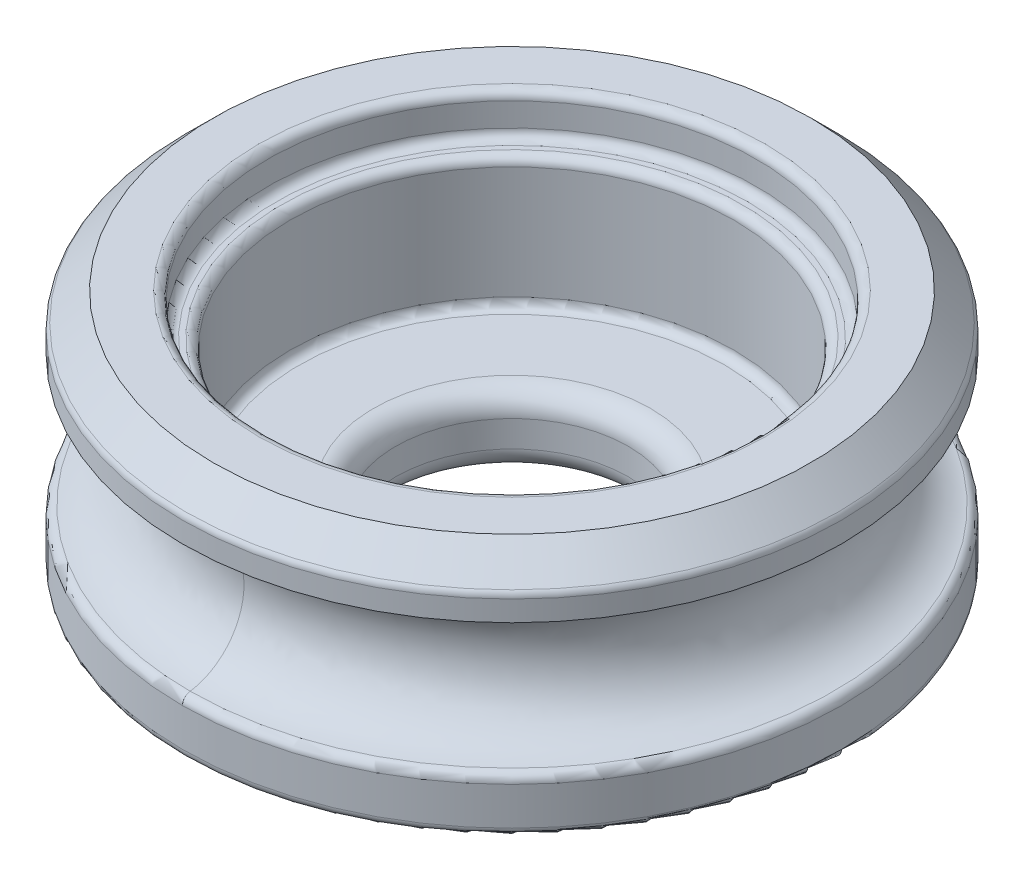
SolidWorks part; units mm, degrees
ref_plane "Front Plane" through (0, 0, 0) normal (0, 0, 1) x (1, 0, 0)
ref_plane "Top Plane" through (0, 0, 0) normal (0, 1, 0) x (1, 0, 0)
ref_plane "Right Plane" through (0, 0, 0) normal (1, 0, 0) x (0, 0, -1)
sketch "Sketch2" plane through (0, 0, 0) normal (0, 1, 0) x (1, 0, 0)
  circle A0 centre (0, 0) radius 6.477 construction
  circle A1 centre (0, 0) radius 9.525
  dimension "D1" = 12.954
  dimension "D2" = 19.05
extrude "Boss-Extrude1" add sketch "Sketch2" along normal blind 6.985
sketch "Sketch3" plane through (0, 6.985, 0) normal (0, 1, 0) x (1, 0, 0)
  circle A0 centre (0, 0) radius 6.4135
  dimension "D1" = 12.827
extrude "Cut-Extrude1" cut sketch "Sketch3" against normal up to surface (6.985 mm away) up to face at (0, 0, 9.525)
sketch "Sketch4" plane through (0, 6.985, 0) normal (0, 1, 0) x (1, 0, 0)
  circle A0 centre (0, 0) radius 7.0723
  dimension "D1" = 14.1446
extrude "Cut-Extrude2" cut sketch "Sketch4" against normal blind 1.1906
ref_plane "Plane1" through (0, 2.8972, 0) normal (0, 1, 0) x (1, 0, 0)
sketch "Sketch6" plane through (0, 0, 0) normal (0, -1, 0) x (1, 0, 0)
  circle A0 centre (0, 0) radius 6.4135
  circle A1 centre (0, 0) radius 3.3655
  circle A2 centre (0, 0) radius 6.4135 construction
  dimension "D1" = 6.731
extrude "Boss-Extrude2" add sketch "Sketch6" against normal blind 2.032
sketch "Sketch7" plane through (0, 0, 0) normal (1, 0, 0) x (0, 0, -1)
  line L0 (9.525, 0) -> (9.525, 6.985) construction
  ellipse E0 centre (9.525, 3.4925) end of major axis (9.525, 5.3975) minor radius 1.778
  dimension "D1" = 3.81
  dimension "D2" = 1.778
sweep "Cut-Sweep2" cut profiles "Sketch7" path edge at (0, 0, 9.525)
fillet "Fillet1" radius 0.254 3 edges at (0, 6.985, 7.0723) (0, 5.7944, 7.0723) (0, 5.7944, 6.4135)
chamfer "Chamfer1" distance 0.889 angle 45 1 edges at (0, 6.985, 9.525)
fillet "Fillet3" radius 0.254 4 edges at (0, 0, 9.525) (9.525, 1.5875, 0) (-9.525, 1.5875, 0) (0, 6.096, 9.525)
fillet "Fillet4" radius 0.635 2 edges at (0, 2.032, -3.3655) (0, 0, -3.3655)
fillet "Fillet5" radius 0.254 1 edges at (0, 2.032, -6.4135)
